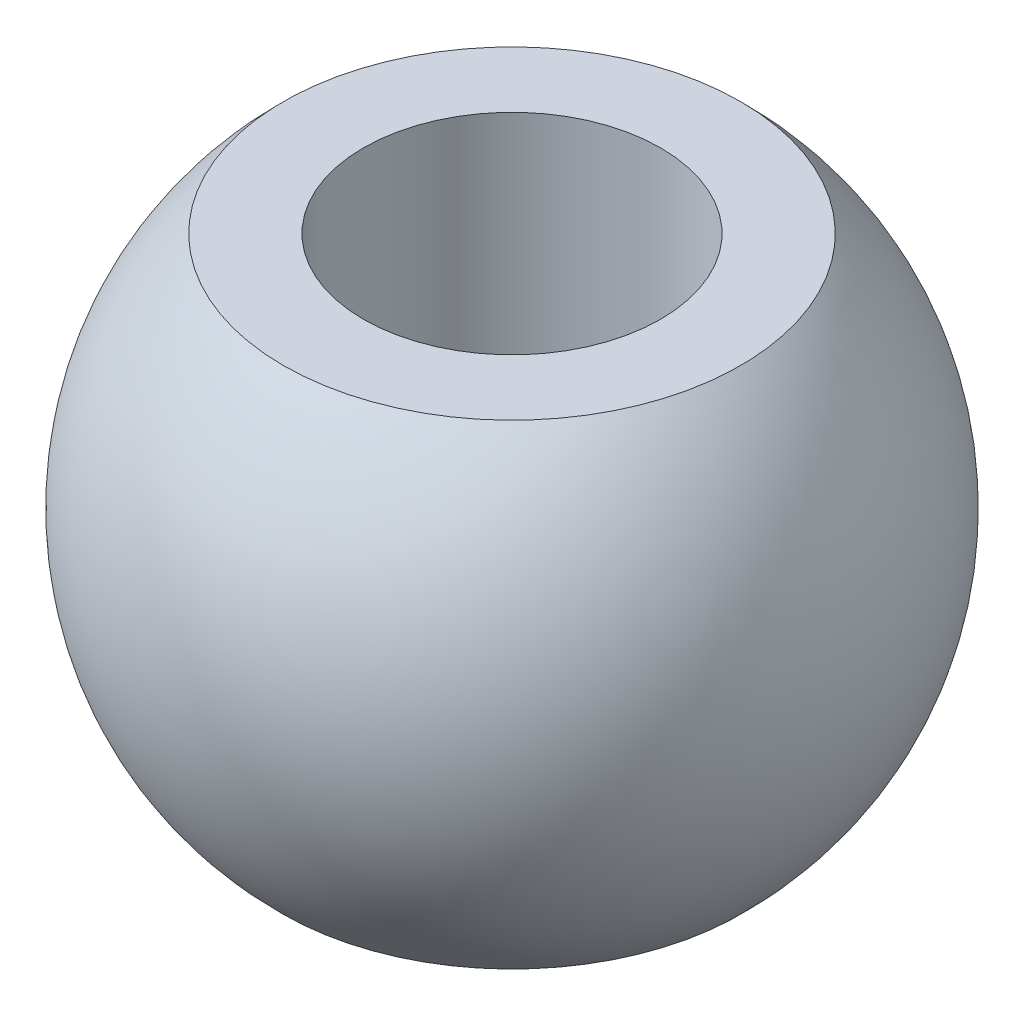
SolidWorks part; units mm, degrees
material "1.0545 (S355N)"
ref_plane "Płaszczyzna przednia" through (0, 0, 0) normal (0, 0, 1) x (1, 0, 0)
ref_plane "Płaszczyzna górna" through (0, 0, 0) normal (0, 1, 0) x (1, 0, 0)
ref_plane "Płaszczyzna prawa" through (0, 0, 0) normal (1, 0, 0) x (0, 0, -1)
sketch "Szkic1" plane through (0, 0, 0) normal (0, 0, 1) x (1, 0, 0)
  line L0 (0, -11.1) -> (0, 11.1) construction
  line L1 (2.5, -4) -> (2.5, 4)
  line L2 (2.5, 4) -> (3.8474, 4)
  line L3 (2.5, -4) -> (3.8474, -4)
  arc A0 (3.8474, -4) -> (3.8474, 4) centre (0, 0) ccw
  point P6 (2.5, 0)
  dimension "d3" = 11.1
  dimension "d1" = 2.5
  dimension "b1" = 8
revolve "Obrót1" add sketch "Szkic1" angle 360 about L0
